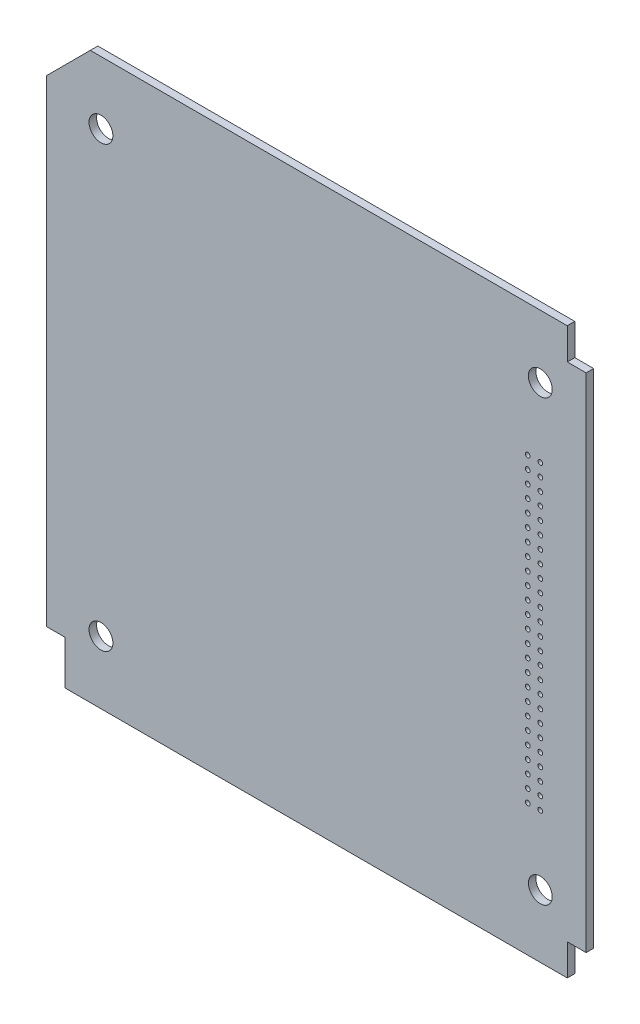
SolidWorks part; units mm, degrees
material "電力回路基板"
ref_plane "正面" through (0, 0, 0) normal (0, 0, 1) x (1, 0, 0)
ref_plane "平面" through (0, 0, 0) normal (0, 1, 0) x (1, 0, 0)
ref_plane "右側面" through (0, 0, 0) normal (1, 0, 0) x (0, 0, -1)
sketch "Sketch1" plane through (0, 0, 0) normal (0, 0, 1) x (1, 0, 0)
  line L0 (-3, 0) -> (-86, 0)
  line L4 (-86, 0) -> (-86, -90)
  line L7 (0, -5) -> (-3, -5)
  line L8 (-3, 0) -> (-3, -5)
  line L11 (0, -85) -> (-3, -85)
  line L12 (-3, -90) -> (-3, -85)
  line L13 (0, -5) -> (0, -85)
  line L14 (-3, -90) -> (-86, -90)
  circle A0 centre (-7.3, -10) radius 1.9
  circle A1 centre (-77.3, -10) radius 1.9
  circle A2 centre (-77.3, -80) radius 1.9
  circle A3 centre (-7.3, -80) radius 1.9
  circle A4 centre (-9.3, -69) radius 0.375
  circle A5 centre (-7.3, -69) radius 0.375
  circle A6 centre (-7.3, -67) radius 0.375
  circle A7 centre (-9.3, -67) radius 0.375
  circle A8 centre (-9.3, -65) radius 0.375
  circle A9 centre (-7.3, -65) radius 0.375
  circle A10 centre (-7.3, -63) radius 0.375
  circle A11 centre (-9.3, -63) radius 0.3838
  circle A12 centre (-9.3, -61) radius 0.375
  circle A13 centre (-7.3, -61) radius 0.375
  circle A14 centre (-7.3, -59) radius 0.375
  circle A15 centre (-9.3, -59) radius 0.375
  circle A16 centre (-7.3, -57) radius 0.375
  circle A17 centre (-9.3, -57) radius 0.375
  circle A18 centre (-9.3, -55) radius 0.375
  circle A19 centre (-7.3, -55) radius 0.375
  circle A20 centre (-7.3, -53) radius 0.375
  circle A21 centre (-9.3, -53) radius 0.375
  circle A22 centre (-9.3, -51) radius 0.375
  circle A23 centre (-7.3, -51) radius 0.375
  circle A24 centre (-7.3, -49) radius 0.375
  circle A25 centre (-9.3, -49) radius 0.375
  circle A26 centre (-9.3, -47) radius 0.375
  circle A27 centre (-7.3, -47) radius 0.375
  circle A28 centre (-7.3, -45) radius 0.375
  circle A29 centre (-9.3, -45) radius 0.3842
  circle A30 centre (-9.3, -43) radius 0.375
  circle A31 centre (-7.3, -43) radius 0.3808
  circle A32 centre (-7.3, -41) radius 0.3774
  circle A33 centre (-9.3, -41) radius 0.3774
  circle A34 centre (-9.3, -39) radius 0.375
  circle A35 centre (-7.3, -39) radius 0.375
  circle A36 centre (-7.3, -37) radius 0.375
  circle A37 centre (-9.3, -37) radius 0.3808
  circle A38 centre (-7.3, -35) radius 0.375
  circle A39 centre (-9.3, -35) radius 0.375
  circle A40 centre (-9.3, -33) radius 0.375
  circle A41 centre (-7.3, -33) radius 0.375
  circle A42 centre (-7.3, -31) radius 0.375
  circle A43 centre (-9.3, -31) radius 0.375
  circle A44 centre (-7.3, -29) radius 0.375
  circle A45 centre (-9.3, -29) radius 0.375
  circle A46 centre (-9.3, -27) radius 0.375
  circle A47 centre (-7.3, -27) radius 0.375
  circle A48 centre (-7.3, -25) radius 0.375
  circle A49 centre (-9.3, -25) radius 0.375
  circle A50 centre (-7.3, -23) radius 0.375
  circle A51 centre (-9.3, -23) radius 0.375
  circle A52 centre (-9.3, -21) radius 0.375
  circle A53 centre (-7.3, -21) radius 0.375
  dimension "D5" = 70
  dimension "D6" = 3
  dimension "D3" = 3.8
  dimension "D10" = 7.3
  dimension "D14" = 10
  dimension "D15" = 10
  dimension "D2" = 90
  dimension "D4" = 70
  dimension "D7" = 5
  dimension "D8" = 86
  dimension "D9" = 7.3
  dimension "D11" = 3
  dimension "D12" = 5
  dimension "D13" = 9.3
  dimension "D16" = 21
extrude "Boss-Extrude1" add sketch "Sketch1" along normal blind 1.2
sketch "ｽｹｯﾁ1" plane through (0, 0, 1.2) normal (0, 0, 1) x (1, 0, 0)
  line L0 (-86, -90) -> (-86, -83)
  line L6 (-86, -7) -> (-86, 0)
  line L8 (-83, -90) -> (-86, -90)
  line L11 (-79, 0) -> (-86, 0)
  line L12 (-86, -7) -> (-79, 0)
  line L13 (-86, -83) -> (-83, -83)
  line L14 (-83, -83) -> (-83, -90)
extrude "ｶｯﾄ - 押し出し1" cut sketch "ｽｹｯﾁ1" against normal blind 10
